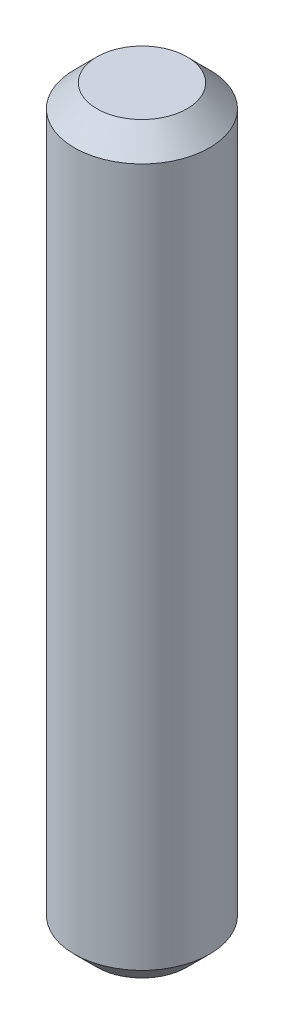
SolidWorks part; units mm, degrees
material "AISI 1045 Stal walcowana na zimno"
ref_plane "Płaszczyzna przednia" through (0, 0, 0) normal (0, 0, 1) x (1, 0, 0)
ref_plane "Płaszczyzna górna" through (0, 0, 0) normal (0, 1, 0) x (1, 0, 0)
ref_plane "Płaszczyzna prawa" through (0, 0, 0) normal (1, 0, 0) x (0, 0, -1)
sketch "Szkic1" plane through (0, 0, 0) normal (0, 1, 0) x (1, 0, 0)
  circle A0 centre (0, 0) radius 3
  dimension "D1" = 6
extrude "Dodanie-wyciągnięcie1" add sketch "Szkic1" along normal blind 33
chamfer "Sfazowanie1" distance 1 angle 45 2 edges at (0, 0, 3) (0, 33, 3)
